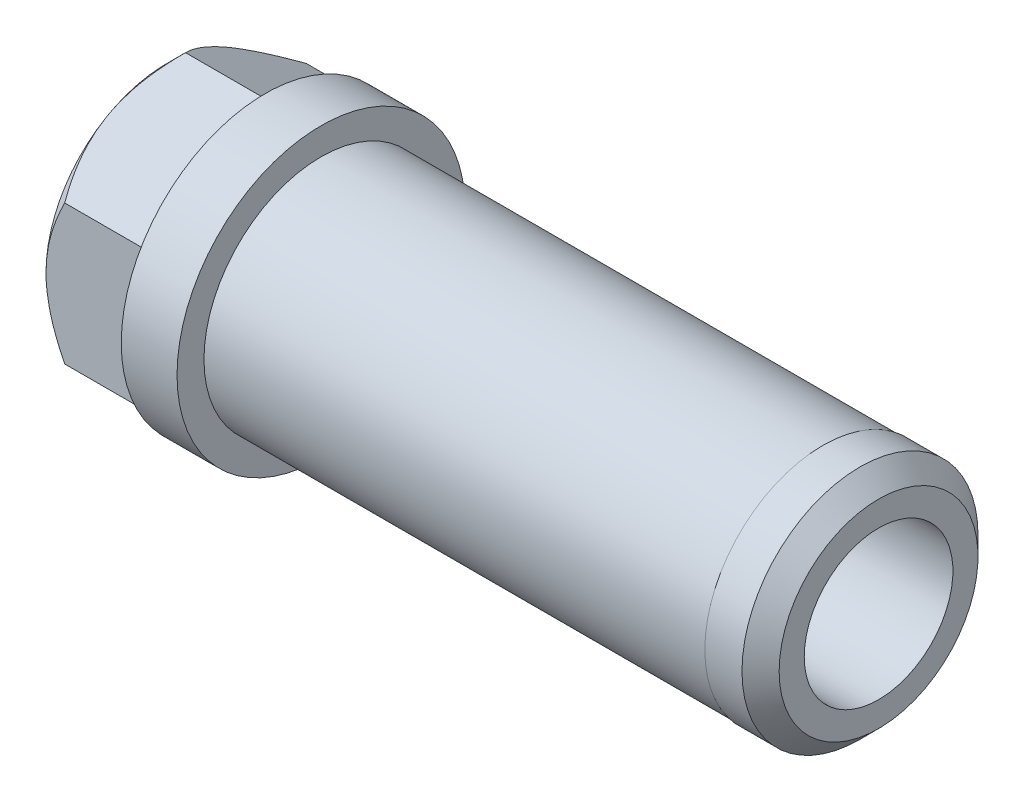
SolidWorks part; units mm, degrees
material "6061-T6 (SS)"
ref_plane "Płaszczyzna XY" through (0, 0, 0) normal (0, 0, 1) x (1, 0, 0)
ref_plane "Płaszczyzna XZ" through (0, 0, 0) normal (0, 1, 0) x (1, 0, 0)
ref_plane "Płaszczyzna YZ" through (0, 0, 0) normal (1, 0, 0) x (0, 0, -1)
sketch "Szkic1" plane through (0, 0, 0) normal (0, 0, 1) x (1, 0, 0)
  line L0 (0, 0) -> (10.2462, 0) construction
  line L1 (0, 4) -> (33, 4)
  line L2 (33, 4) -> (33, 6.35)
  line L3 (33, 6.35) -> (3, 6.35)
  line L4 (3, 6.35) -> (3, 7.75)
  line L5 (3, 7.75) -> (0, 7.75)
  line L6 (0, 7.75) -> (0, 4)
  dimension "D1" = 3
  dimension "D2" = 30
  dimension "D3" = 8
  dimension "D4" = 15.5
  dimension "D5" = 12.7
revolve "Obrót1" add sketch "Szkic1" angle 360 about L0
chamfer "Sfazowanie2" distance 1 angle 45 1 edges at (33, 0, 6.35)
sketch "Szkic2" plane through (0, 0, 0) normal (0, 0, 1) x (1, 0, 0)
  line L0 (3, 7.75) -> (3, 6.35)
  line L1 (3, -6.35) -> (3, -7.75)
  line L2 (3, -6.35) -> (3, -7.75)
  line L3 (3, 7.75) -> (3, 6.35)
  line L4 (33, 5.35) -> (32, 6.35)
  line L5 (32, -6.35) -> (33, -5.35)
  line L6 (32, -6.35) -> (33, -5.35)
  line L7 (33, 5.35) -> (32, 6.35)
  line L8 (3, 0) -> (30.8109, 0) construction
  line L9 (3, 6.35) -> (30, 6.35)
  line L10 (3, 6.35) -> (3, 6.3)
  line L11 (3, 6.3) -> (30, 6.3)
  line L12 (30, 6.35) -> (30, 6.3)
  dimension "D1" = 2
  dimension "D2" = 0.05
revolve "Wycięcie-obrót1" cut sketch "Szkic2" angle 360 about L8
sketch "Szkic3" plane through (0, 0, 0) normal (-1, 0, 0) x (0, 0, 1)
  line L1 (6.5, -3.7528) -> (6.5, 3.7528)
  line L2 (6.5, 3.7528) -> (0, 7.5056)
  line L3 (0, 7.5056) -> (-6.5, 3.7528)
  line L4 (-6.5, 3.7528) -> (-6.5, -3.7528)
  line L5 (-6.5, -3.7528) -> (0, -7.5056)
  line L6 (0, -7.5056) -> (6.5, -3.7528)
  circle A0 centre (0, 0) radius 6.5 construction
  circle A1 centre (0, 0) radius 4
  circle A2 centre (0, 0) radius 4 construction
  dimension "D1" = 13
extrude "Dodanie-wyciągnięcie1" add sketch "Szkic3" along normal blind 5.3
sketch "Szkic4" plane through (0, 0, 0) normal (0, 1, 0) x (1, 0, 0)
  line L0 (-5.3, 6.5) -> (-5.3, 10)
  line L1 (-5.3, 10) -> (-1.8, 10)
  line L2 (-1.8, 10) -> (-5.3, 6.5)
  line L3 (0, 0) -> (-4.9952, 0) construction
  dimension "D1" = 45
  dimension "D2" = 10
revolve "Wycięcie-obrót2" cut sketch "Szkic4" angle 360 about L3
sketch "Szkic5" [suppressed] plane through (0, 0, 0) normal (0, 0, 1) x (1, 0, 0)
  line L0 (0, 9.815) -> (0, 7.75)
  line L1 (0, -7.75) -> (0, -9.815)
  line L2 (0, -8.815) -> (0, -9.815)
  line L4 (-1, -9.815) -> (0, -8.815)
  line L5 (-1, -9.815) -> (0, -9.815)
  line L6 (0, 0) -> (10.6319, 0) construction
  dimension "D1" = 45
  dimension "D2" = 1
revolve "Wycięcie-obrót3" [suppressed] cut sketch "Szkic5" angle 360 about L6
chamfer "Sfazowanie3" distance 0.5 angle 45 1 edges at (-5.3, 0, 4)
